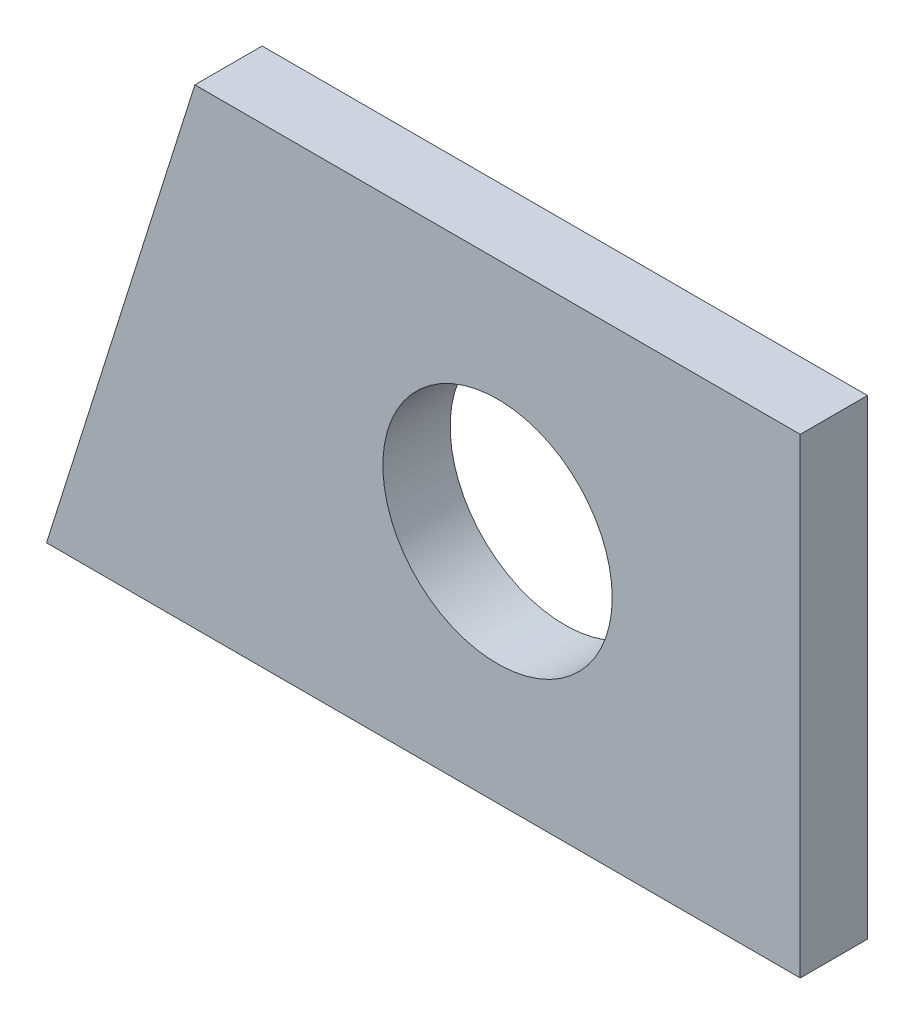
SolidWorks part; units mm, degrees
ref_plane "Front Plane" through (0, 0, 0) normal (0, 0, 1) x (1, 0, 0)
ref_plane "Top Plane" through (0, 0, 0) normal (0, 1, 0) x (1, 0, 0)
ref_plane "Right Plane" through (0, 0, 0) normal (1, 0, 0) x (0, 0, -1)
sketch "Sketch1" plane through (0, 0, 0) normal (0, 0, 1) x (1, 0, 0)
  line L0 (-3.3971, 3.5) -> (-5.6029, -3.5)
  line L1 (-5.6029, -3.5) -> (5.6029, -3.5)
  line L2 (5.6029, -3.5) -> (5.6029, 3.5)
  line L3 (5.6029, 3.5) -> (-3.3971, 3.5)
  circle A0 centre (1.1029, 0) radius 1.705
  dimension "D2" = 3.41
  dimension "D1" = 9
  dimension "D3" = 7
  dimension "D4" = 107.49
  dimension "D5" = 3.5
  dimension "D6" = 4.5
extrude "Boss-Extrude1" add sketch "Sketch1" along normal blind 1
